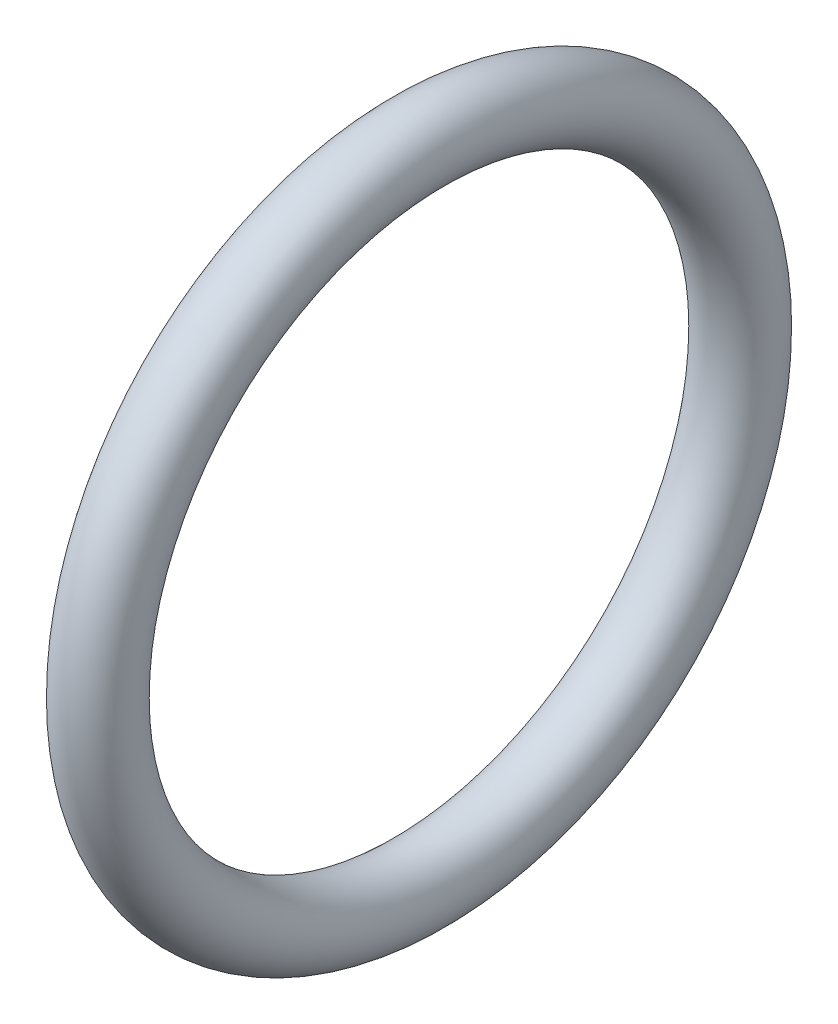
SolidWorks part; units mm, degrees
ref_plane "Front Plane" through (0, 0, 0) normal (0, 0, 1) x (1, 0, 0)
ref_plane "Top Plane" through (0, 0, 0) normal (0, 1, 0) x (1, 0, 0)
ref_plane "Right Plane" through (0, 0, 0) normal (1, 0, 0) x (0, 0, -1)
sketch "Sketch1" [suppressed] plane through (0, 0, 0) normal (0, 0, 1) x (1, 0, 0)
  line L0 (-43.7166, 0) -> (79.6876, 0) construction
  line L2 (0, -13.462) -> (1.524, -13.462)
  line L3 (0, -13.462) -> (0, -18.161)
  line L4 (0, -18.161) -> (1.524, -18.161)
  line L5 (1.524, -13.462) -> (1.524, -18.161)
  dimension "A" = 15.24
  dimension "B" = 19.05
  dimension "C" = 2.032
revolve "Revolve1" [suppressed] add sketch "Sketch1" angle 360 about L0
sketch "Sketch2" plane through (0, 0, 0) normal (0, 0, 1) x (1, 0, 0)
  line L0 (-34.685, 0) -> (47.6686, 0) construction
  circle A0 centre (2.54, -6.731) radius 0.762
  dimension "D1" = 2.54
  dimension "E" = 1.524
  dimension "D" = 11.938
revolve "Revolve3" add sketch "Sketch2" angle 360 about L0
